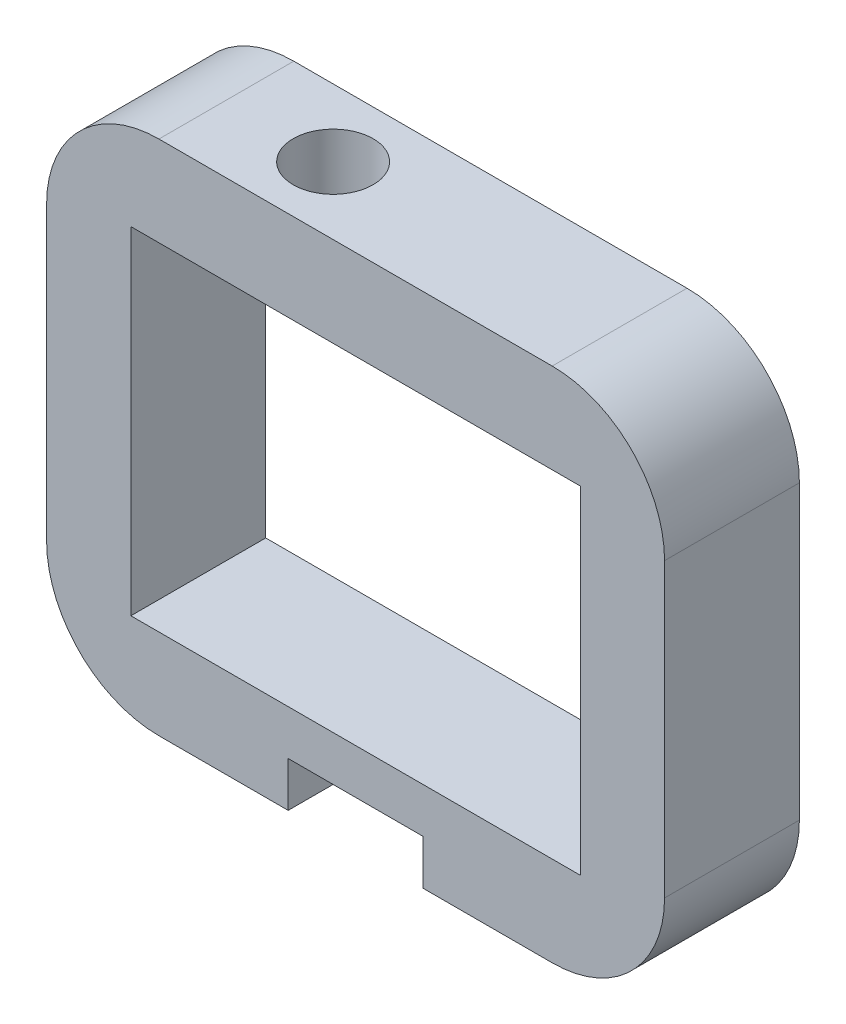
SolidWorks part; units mm, degrees
ref_plane "Front Plane" through (0, 0, 0) normal (0, 0, 1) x (1, 0, 0)
ref_plane "Top Plane" through (0, 0, 0) normal (0, 1, 0) x (1, 0, 0)
ref_plane "Right Plane" through (0, 0, 0) normal (1, 0, 0) x (0, 0, -1)
sketch "Sketch1" plane through (0, 0, 0) normal (0, 0, 1) x (1, 0, 0)
  line L1 (-27.5, -23) -> (-27.5, 23)
  line L4 (20, 15) -> (-20, 15)
  line L5 (-20, 15) -> (-20, -15)
  line L6 (-20, -15) -> (20, -15)
  line L7 (20, -15) -> (20, 15)
  line L8 (27.5, 23) -> (27.5, -23)
  line L11 (-27.5, -23) -> (27.5, 23) construction
  line L12 (27.5, 23) -> (-27.5, 23)
  line L13 (-27.5, -23) -> (27.5, -23)
  point P11 (0, 0)
  dimension "D1" = 40
  dimension "D2" = 55
  dimension "D3" = 8
  dimension "D4" = 46
  dimension "D5" = 8
  dimension "D6" = 7.5
extrude "Boss-Extrude1" add sketch "Sketch1" along normal mid plane 12
sketch "Sketch3" plane through (0, 0, 0) normal (0, 1, 0) x (1, 0, 0)
  line L0 (-41.8631, 0) -> (39.4729, 0) construction
  line L1 (27.5, 0) -> (-8, 0) construction
  line L2 (27.5, -6) -> (27.5, 6) construction
  circle A0 centre (-8, 0) radius 3.556
  dimension "D1" = 7.112
  dimension "D2" = 8
  dimension "D3" = 35.5
extrude "Cut-Extrude1" cut sketch "Sketch3" along normal through all
sketch "Sketch6" plane through (0, -23, 0) normal (0, -1, 0) x (1, 0, 0)
  line L0 (-27.5, 6) -> (27.5, 6) construction
  line L1 (-6, 6) -> (6, 6)
  line L2 (-6, 6) -> (-6, -6)
  line L3 (-6, -6) -> (6, -6)
  line L4 (6, 6) -> (6, -6)
  line L5 (-27.5, -6) -> (27.5, -6) construction
  line L6 (-6, -6) -> (6, 6) construction
  point P8 (0, 0)
  dimension "D1" = 12
extrude "Cut-Extrude4" cut sketch "Sketch6" against normal blind 4
fillet "Fillet1" radius 10 4 edges at (-27.5, -23, 0) (27.5, -23, 0) (27.5, 23, 0) (-27.5, 23, 0)
